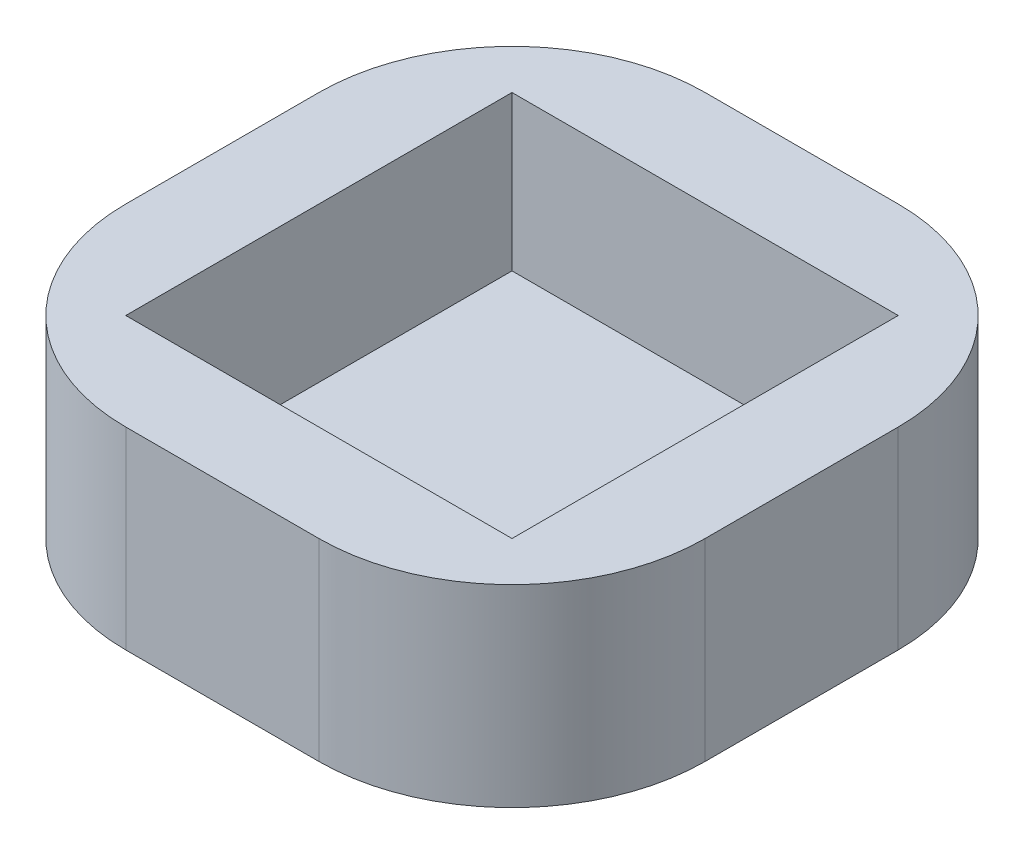
SolidWorks part; units mm, degrees
ref_plane "Front Plane" through (0, 0, 0) normal (0, 0, 1) x (1, 0, 0)
ref_plane "Top Plane" through (0, 0, 0) normal (0, 1, 0) x (1, 0, 0)
ref_plane "Right Plane" through (0, 0, 0) normal (1, 0, 0) x (0, 0, -1)
sketch "Sketch1" plane through (0, 0, 0) normal (0, 1, 0) x (1, 0, 0)
  line L1 (-26.3921, 9.3506) -> (-16.3921, 9.3506)
  line L2 (-36.3921, -0.6494) -> (-36.3921, -10.6494)
  line L3 (-26.3921, -20.6494) -> (-16.3921, -20.6494)
  line L4 (-6.3921, -0.6494) -> (-6.3921, -10.6494)
  arc A0 (-36.3921, -10.6494) -> (-26.3921, -20.6494) centre (-26.3921, -10.6494) ccw
  arc A1 (-26.3921, 9.3506) -> (-36.3921, -0.6494) centre (-26.3921, -0.6494) ccw
  arc A2 (-16.3921, -20.6494) -> (-6.3921, -10.6494) centre (-16.3921, -10.6494) ccw
  arc A3 (-16.3921, 9.3506) -> (-6.3921, -0.6494) centre (-16.3921, -0.6494) cw
  dimension "D1" = 10
  dimension "D2" = 10
  dimension "D3" = 10
  dimension "D4" = 10
  dimension "D5" = 30
  dimension "D6" = 30
extrude "Boss-Extrude1" add sketch "Sketch1" along normal blind 10
sketch "Sketch2" plane through (0, 10, 0) normal (0, 1, 0) x (-1, 0, 0)
  line L0 (26.3921, 20.6494) -> (16.3921, 20.6494) construction
  line L1 (31.3921, -4.3506) -> (11.3921, -4.3506)
  line L2 (31.3921, -4.3506) -> (31.3921, 15.6494)
  line L3 (31.3921, 15.6494) -> (11.3921, 15.6494)
  line L4 (11.3921, -4.3506) -> (11.3921, 15.6494)
  line L5 (6.3921, 10.6494) -> (6.3921, 0.6494) construction
  dimension "D1" = 20
  dimension "D2" = 20
  dimension "D3" = 5
  dimension "D4" = 5
extrude "Cut-Extrude1" cut sketch "Sketch2" against normal blind 8
